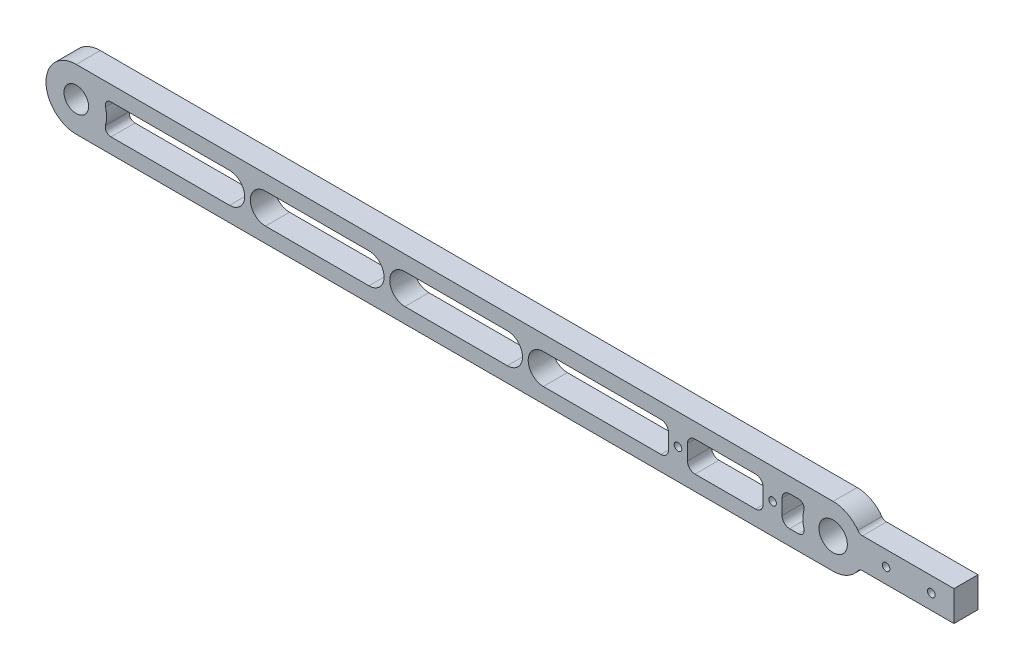
SolidWorks part; units mm, degrees
ref_plane "Front Plane" through (0, 0, 0) normal (0, 0, 1) x (1, 0, 0)
ref_plane "Top Plane" through (0, 0, 0) normal (0, 1, 0) x (1, 0, 0)
ref_plane "Right Plane" through (0, 0, 0) normal (1, 0, 0) x (0, 0, -1)
ref_plane "Plane1" through (0, 0, 0) normal (0, 0, -1) x (-1, 0, 0)
sketch "Sketch1" plane through (0, 0, 0) normal (0, 0, -1) x (-1, 0, 0)
  line L0 (-186.5, 2) -> (-186.5, -2)
  line L1 (-188.5, -4) -> (-190.8348, -4)
  line L2 (-190.8348, 4) -> (-188.5, 4)
  line L3 (-181.5, -2) -> (-181.5, 2)
  line L4 (-179.5, 4) -> (-163.5, 4)
  line L5 (-161.5, 2) -> (-161.5, -2)
  line L6 (-163.5, -4) -> (-179.5, -4)
  line L7 (-49.9989, -4) -> (-77.3326, -4)
  line L8 (-77.3326, 4) -> (-49.9989, 4)
  line L9 (-123.4163, -4) -> (-154.5, -4)
  line L10 (-156.5, -2) -> (-156.5, 2)
  line L11 (-154.5, 4) -> (-123.4163, 4)
  line L12 (-113.9163, 4) -> (-86.8326, 4)
  line L13 (-86.8326, -4) -> (-113.9163, -4)
  line L14 (-40.4989, 4) -> (-9.1652, 4)
  line L15 (-9.1652, -4) -> (-40.4989, -4)
  line L16 (0, 8) -> (-200, 8)
  line L17 (-207.746, 4) -> (-231.9282, 4)
  line L18 (-231.9282, 4) -> (-231.9282, -4)
  line L19 (-231.9282, -4) -> (-207.746, -4)
  line L20 (-200, -8) -> (0, -8)
  circle A0 centre (-159, 0) radius 1
  circle A1 centre (-184, 0) radius 1
  circle A2 centre (0, 0) radius 3.25
  arc A3 (-188.5, 4) -> (-186.5, 2) centre (-188.5, 2) cw
  arc A4 (-186.5, -2) -> (-188.5, -4) centre (-188.5, -2) cw
  arc A5 (-190.8348, -4) -> (-192.282, -2.1053) centre (-190.8348, -2.5) cw
  arc A6 (-192.282, -2.1053) -> (-192.282, 2.1053) centre (-200, 0) ccw
  arc A7 (-192.282, 2.1053) -> (-190.8348, 4) centre (-190.8348, 2.5) cw
  circle A8 centre (-200, 0) radius 3.75
  circle A9 centre (-213.9821, 0) radius 1
  circle A10 centre (-225.9462, 0) radius 1
  arc A11 (-179.5, -4) -> (-181.5, -2) centre (-179.5, -2) cw
  arc A12 (-181.5, 2) -> (-179.5, 4) centre (-179.5, 2) cw
  arc A13 (-163.5, 4) -> (-161.5, 2) centre (-163.5, 2) cw
  arc A14 (-161.5, -2) -> (-163.5, -4) centre (-163.5, -2) cw
  arc A15 (-49.9989, 4) -> (-49.9989, -4) centre (-49.9989, 0) cw
  arc A16 (-77.3326, -4) -> (-77.3326, 4) centre (-77.3326, 0) cw
  arc A17 (-123.4163, 4) -> (-123.4163, -4) centre (-123.4163, 0) cw
  arc A18 (-154.5, -4) -> (-156.5, -2) centre (-154.5, -2) cw
  arc A19 (-156.5, 2) -> (-154.5, 4) centre (-154.5, 2) cw
  arc A20 (-113.9163, -4) -> (-113.9163, 4) centre (-113.9163, 0) cw
  arc A21 (-86.8326, 4) -> (-86.8326, -4) centre (-86.8326, 0) cw
  arc A22 (-40.4989, -4) -> (-40.4989, 4) centre (-40.4989, 0) cw
  arc A23 (-9.1652, 4) -> (-7.718, 2.1053) centre (-9.1652, 2.5) cw
  arc A24 (-7.718, 2.1053) -> (-7.718, -2.1053) centre (0, 0) ccw
  arc A25 (-7.718, -2.1053) -> (-9.1652, -4) centre (-9.1652, -2.5) cw
  arc A26 (0, -8) -> (0, 8) centre (0, 0) ccw
  arc A27 (-200, 8) -> (-206.5229, 4.6316) centre (-200, 0) ccw
  arc A28 (-206.5229, 4.6316) -> (-207.746, 4) centre (-207.746, 5.5) cw
  arc A29 (-207.746, -4) -> (-206.5229, -4.6316) centre (-207.746, -5.5) cw
  arc A30 (-206.5229, -4.6316) -> (-200, -8) centre (-200, 0) ccw
extrude "Boss-Extrude1" add sketch "Sketch1" against normal blind 6.35
